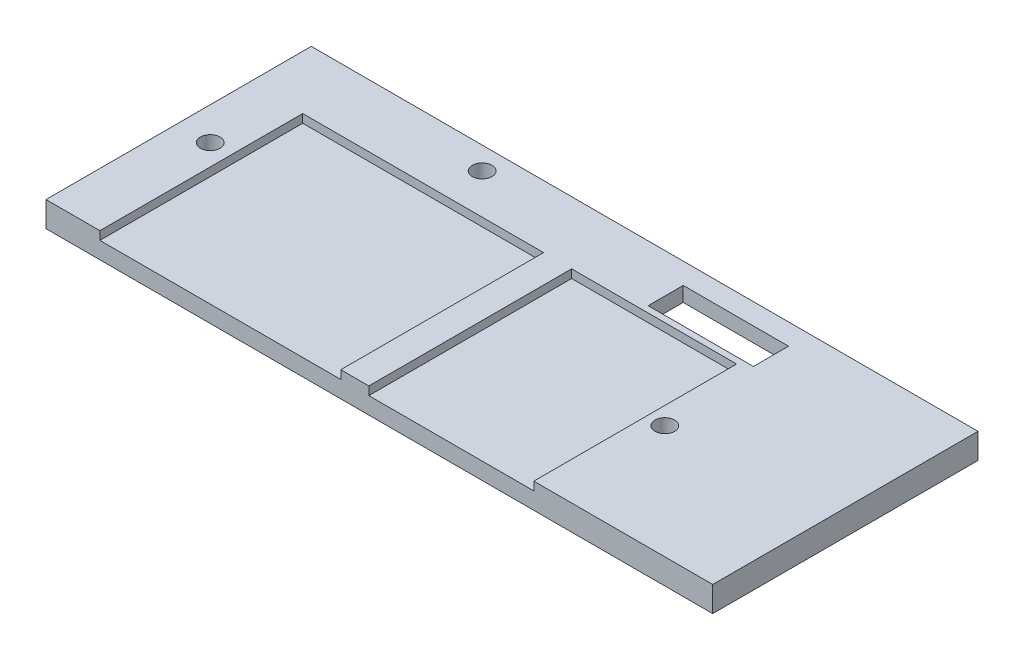
SolidWorks part; units mm, degrees
ref_plane "前视基准面" through (0, 0, 0) normal (0, 0, 1) x (1, 0, 0)
ref_plane "上视基准面" through (0, 0, 0) normal (0, 1, 0) x (1, 0, 0)
ref_plane "右视基准面" through (0, 0, 0) normal (1, 0, 0) x (0, 0, -1)
sketch "Sketch1" plane through (0, 0, 0) normal (0, 1, 0) x (1, 0, 0)
  line L1 (-47.5, 18.9) -> (47.5, 18.9)
  line L2 (-47.5, 18.9) -> (-47.5, -18.9)
  line L3 (-47.5, -18.9) -> (47.5, -18.9)
  line L4 (47.5, 18.9) -> (47.5, -18.9)
  line L5 (-47.5, 18.9) -> (47.5, -18.9) construction
  line L6 (-47.5, -18.9) -> (47.5, 18.9) construction
  point P0 (0, 0)
extrude "Boss-Extrude1" add sketch "Sketch1" along normal blind 3.6
sketch "Sketch2" plane through (0, 3.6, 0) normal (0, 1, 0) x (1, 0, 0)
  circle A0 centre (-42.82, -0.18) radius 1.4
  circle A1 centre (-19.96, 15.7) radius 1.4
  circle A2 centre (24.5, -2.72) radius 1.4
extrude "Cut-Extrude1" cut sketch "Sketch2" against normal blind 4
sketch "Sketch3" plane through (0, 0, 0) normal (0, -1, 0) x (1, 0, 0)
  line L0 (-40.82, -6.62) -> (-34.82, -6.62)
  line L1 (28, -18.9) -> (7, -18.9)
  line L2 (-19.26, -6.1) -> (-19.26, 15.9)
  line L3 (22.74, 15.9) -> (-19.26, 15.9)
  line L4 (11, -8.9) -> (7, -8.9)
  line L5 (45.5, -16.9) -> (38.5, -16.9)
  line L6 (45.5, -16.9) -> (45.5, -11.9)
  line L7 (45.5, -11.9) -> (38.5, -11.9)
  line L8 (38.5, -16.9) -> (38.5, -11.9)
  line L9 (-19.26, -6.1) -> (22.74, -6.1)
  line L10 (22.74, -6.1) -> (22.74, 1.32)
  line L11 (-17.26, -13.9) -> (-12.26, -13.9)
  line L12 (24.5, 1.32) -> (22.74, 1.32)
  line L13 (-12.26, -18.9) -> (-12.26, -13.9)
  line L18 (-17.26, -18.9) -> (-17.26, -13.9)
  line L19 (24.5, 4.12) -> (22.74, 4.12)
  line L20 (7, -18.9) -> (7, -8.9)
  line L21 (11, -8.9) -> (28, -8.9)
  line L22 (28, -8.9) -> (28, -18.9)
  line L23 (47.5, -18.9) -> (-47.5, -18.9) construction
  line L24 (-34.82, -6.62) -> (-34.82, -12.62)
  line L25 (22.74, 4.12) -> (22.74, 15.9)
  line L26 (-40.82, -12.62) -> (-34.82, -12.62)
  line L27 (-40.82, -6.62) -> (-40.82, -12.62)
  line L30 (-12.26, -18.9) -> (-17.26, -18.9)
  circle A0 centre (24.5, 2.72) radius 1.4 construction
  arc A1 (24.5, 1.32) -> (24.5, 4.12) centre (24.5, 2.72) ccw
  point P27 (-12.26, -16.4)
  point P30 (-17.26, -16.4)
extrude "Cut-Extrude5" cut sketch "Sketch3" against normal blind 1.5
sketch "Sketch4" plane through (0, 1.5, 0) normal (0, -1, 0) x (1, 0, 0)
  line L0 (22.74, 4.12) -> (22.74, 15.9) construction
  line L1 (22.74, 4.12) -> (22.74, 15.9)
  line L3 (20.74, 4.12) -> (20.74, 15.9)
  line L4 (20.74, 4.12) -> (20.74, -6.1)
  line L5 (-19.26, -6.1) -> (22.74, -6.1) construction
  line L6 (20.74, -6.1) -> (22.74, -6.1)
  line L7 (22.74, -6.1) -> (22.74, 1.32)
  line L8 (22.74, 1.32) -> (24.5, 1.32)
  line L9 (24.5, 4.12) -> (22.74, 4.12) construction
  line L10 (24.5, 4.12) -> (22.74, 4.12)
  line L11 (22.74, 15.9) -> (20.74, 15.9)
  arc A1 (24.5, 4.12) -> (24.5, 1.32) centre (24.5, 2.72) ccw construction
  arc A2 (24.5, 4.12) -> (24.5, 1.32) centre (24.5, 2.72) ccw
  dimension "D1" = 2
extrude "Boss-Extrude3" add sketch "Sketch4" along normal blind 1.5
sketch "Sketch6" plane through (0, 3.6, 0) normal (0, 1, 0) x (1, 0, 0)
  line L2 (8.5, 10.9) -> (8.5, 15.9)
  line L3 (23.5, 10.9) -> (23.5, 15.9)
  line L6 (23.5, 15.9) -> (8.5, 15.9)
  line L7 (23.5, 10.9) -> (8.5, 10.9)
  line L8 (47.5, 10.9) -> (-47.5, 10.9) construction
  line L9 (47.5, 15.9) -> (-47.5, 15.9) construction
  line L11 (23.5, -18.9) -> (23.5, 18.9) construction
  line L12 (8.5, -18.9) -> (8.5, 18.9) construction
  dimension "D1" = 15
  dimension "D2" = 5
extrude "Cut-Extrude6" cut sketch "Sketch6" against normal blind 18.5
sketch "Sketch7" plane through (28, 0, 0) normal (-1, 0, 0) x (0, 0, 1)
  line L1 (-18.9, 1.5) -> (-8.9, 1.5)
  line L2 (-18.9, 1.5) -> (-18.9, 0)
  line L3 (-18.9, 0) -> (-8.9, 0)
  line L4 (-8.9, 1.5) -> (-8.9, 0)
extrude "Cut-Extrude7" cut sketch "Sketch7" against normal blind 2
sketch "Sketch9" plane through (0, 0, -8.9) normal (0, 0, -1) x (-1, 0, 0)
  line L1 (-30, 1.5) -> (-7, 1.5)
  line L2 (-30, 1.5) -> (-30, 0)
  line L3 (-30, 0) -> (-7, 0)
  line L4 (-7, 1.5) -> (-7, 0)
extrude "Cut-Extrude8" cut sketch "Sketch9" against normal blind 1.5
sketch "Sketch10" plane through (0, 1.5, 0) normal (0, -1, 0) x (1, 0, 0)
  line L1 (30, -18.9) -> (12, -18.9)
  line L2 (30, -18.9) -> (30, -17.4)
  line L3 (30, -17.4) -> (12, -17.4)
  line L4 (12, -18.9) -> (12, -17.4)
  dimension "D1" = 1.5
  dimension "D2" = 18
extrude "Boss-Extrude5" add sketch "Sketch10" along normal up to surface (1.5 mm away) up to face at (0.74, 0, 4.9)
sketch "Sketch11" plane through (0, 3.6, 0) normal (0, 1, 0) x (1, 0, 0)
  line L0 (-39.82, 10) -> (-39.82, -18.9)
  line L2 (-39.82, -18.9) -> (-5.5, -18.9)
  line L4 (-39.82, 10) -> (-5.5, 10)
  line L6 (-1.5, -18.9) -> (22, -18.9)
  line L9 (22, 10) -> (22, -18.9)
  line L10 (-5.5, 10) -> (-5.5, -18.9)
  line L11 (-1.5, 10) -> (-1.5, -18.9)
  line L12 (-1.5, 10) -> (22, 10)
extrude "Cut-Extrude10" cut sketch "Sketch11" against normal blind 1.2
sketch "Sketch12" plane through (12, 0, 0) normal (-1, 0, 0) x (0, 0, 1)
  line L1 (-18.9, 1.5) -> (-17.4, 1.5)
  line L2 (-18.9, 1.5) -> (-18.9, 0)
  line L3 (-18.9, 0) -> (-17.4, 0)
  line L4 (-17.4, 1.5) -> (-17.4, 0)
extrude "Boss-Extrude6" add sketch "Sketch12" along normal blind 0.5
